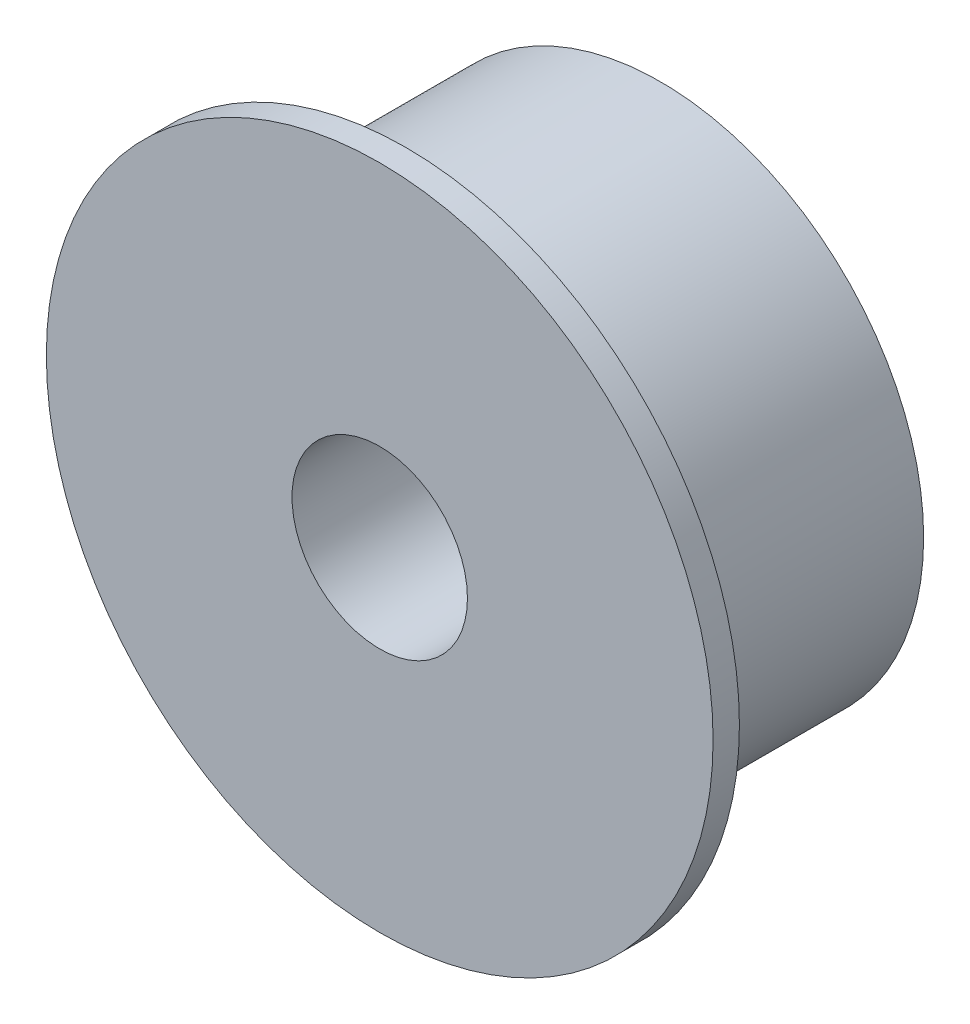
SolidWorks part; units mm, degrees
ref_plane "Front Plane" through (0, 0, 0) normal (0, 0, 1) x (1, 0, 0)
ref_plane "Top Plane" through (0, 0, 0) normal (0, 1, 0) x (1, 0, 0)
ref_plane "Right Plane" through (0, 0, 0) normal (1, 0, 0) x (0, 0, -1)
sketch "Sketch1" plane through (0, 0, 0) normal (0, 0, 1) x (1, 0, 0)
  circle A0 centre (0, 0) radius 2.5
  circle A1 centre (0, 0) radius 7.5
  dimension "D1" = 5
  dimension "D2" = 15
extrude "Boss-Extrude1" add sketch "Sketch1" along normal blind 8
sketch "Sketch2" plane through (0, 0, 8) normal (0, 0, 1) x (1, 0, 0)
  circle A0 centre (0, 0) radius 5
  circle A1 centre (0, 0) radius 9.5
  circle A2 centre (0, 0) radius 7.5 construction
  dimension "D1" = 2
extrude "Boss-Extrude2" add sketch "Sketch2" against normal blind 0.75
